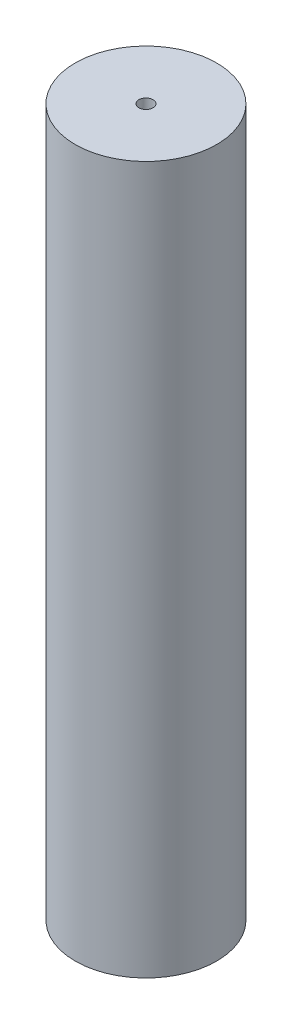
SolidWorks part; units mm, degrees
ref_plane "Front Plane" through (0, 0, 0) normal (0, 0, 1) x (1, 0, 0)
ref_plane "Top Plane" through (0, 0, 0) normal (0, 1, 0) x (1, 0, 0)
ref_plane "Right Plane" through (0, 0, 0) normal (1, 0, 0) x (0, 0, -1)
sketch "Sketch1" plane through (0, 0, 0) normal (0, 1, 0) x (1, 0, 0)
  circle A0 centre (0, 0) radius 100
extrude "Boss-Extrude2" add sketch "Sketch1" along normal blind 1000
sketch "Sketch2" plane through (0, 1000, 0) normal (0, 1, 0) x (1, 0, 0)
  circle A0 centre (0, 0) radius 10
extrude "Cut-Extrude1" cut sketch "Sketch2" against normal blind 20
